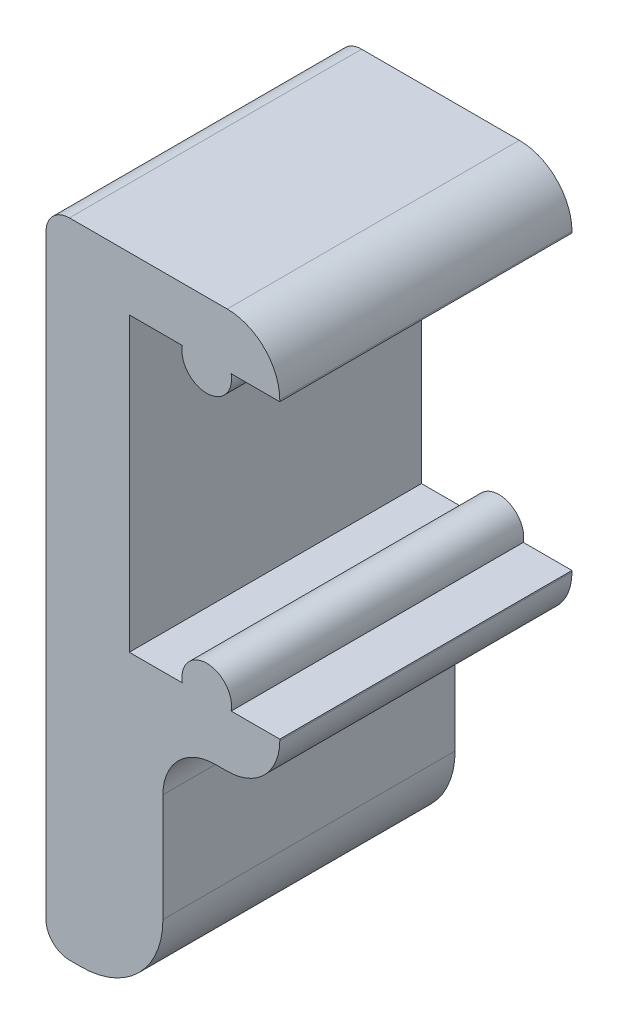
SolidWorks part; units mm, degrees
ref_plane "Front Plane" through (0, 0, 0) normal (0, 0, 1) x (1, 0, 0)
ref_plane "Top Plane" through (0, 0, 0) normal (0, 1, 0) x (1, 0, 0)
ref_plane "Right Plane" through (0, 0, 0) normal (1, 0, 0) x (0, 0, -1)
sketch "Sketch4" plane through (0, 0, 0) normal (0, 0, 1) x (1, 0, 0)
  line L0 (0, 0.8) -> (0, 21.2)
  line L1 (0.8, 22) -> (6.2, 22)
  line L2 (8, 20.2) -> (8, 20.15)
  line L3 (1.2, 0) -> (0.8, 0)
  line L4 (8, 20.15) -> (2.85, 20.15)
  line L5 (2.85, 20.15) -> (2.85, 10.15)
  line L6 (2.85, 10.15) -> (8, 10.15)
  line L10 (5.5, 20.15) -> (5.5, 16.9827) construction
  line L13 (4, 6.5) -> (4, 2.8)
  line L14 (8, 10.15) -> (8, 10.1)
  line L15 (6.2, 8.3) -> (5.8, 8.3)
  line L16 (2.85, 15.15) -> (11.672, 15.15) construction
  arc A2 (4.6633, 20.15) -> (6.3367, 20.15) centre (5.5, 20) ccw
  arc A3 (4.6633, 10.15) -> (6.3367, 10.15) centre (5.5, 10.3) cw
  arc A4 (8, 20.2) -> (6.2, 22) centre (6.2, 20.2) ccw
  arc A5 (6.2, 8.3) -> (8, 10.1) centre (6.2, 10.1) ccw
  arc A6 (4, 2.8) -> (1.2, 0) centre (1.2, 2.8) cw
  arc A7 (4, 6.5) -> (5.8, 8.3) centre (5.8, 6.5) cw
  arc A8 (0, 21.2) -> (0.8, 22) centre (0.8, 21.2) cw
  arc A9 (0.8, 0) -> (0, 0.8) centre (0.8, 0.8) cw
  point P7 (2.85, 15.15)
  point P15 (8, 22)
  point P26 (8, 22)
  point P29 (8, 8.3)
  point P32 (4, 0)
  point P37 (0, 22)
  point P40 (0, 0)
  dimension "D6" = 4
  dimension "D8" = 0.15
  dimension "D9" = 0.85
  dimension "D11" = 1.8
  dimension "D12" = 1.8
  dimension "D13" = 2.8
  dimension "D14" = 1.8
  dimension "D15" = 0.8
  dimension "D16" = 0.8
  dimension "D1" = 22
  dimension "D2" = 8
  dimension "D3" = 1.85
  dimension "D4" = 2.85
  dimension "D5" = 10
  dimension "D7" = 1.85
  dimension "D10" = 2.65
extrude "Boss-Extrude1" add sketch "Sketch4" along normal blind 10 contours A9 L3 A6 L13 A7 L15 A5 L14 L6 L5 L4 L2 A4 L1 A8 L0 | L4 A2 | A3 L6
